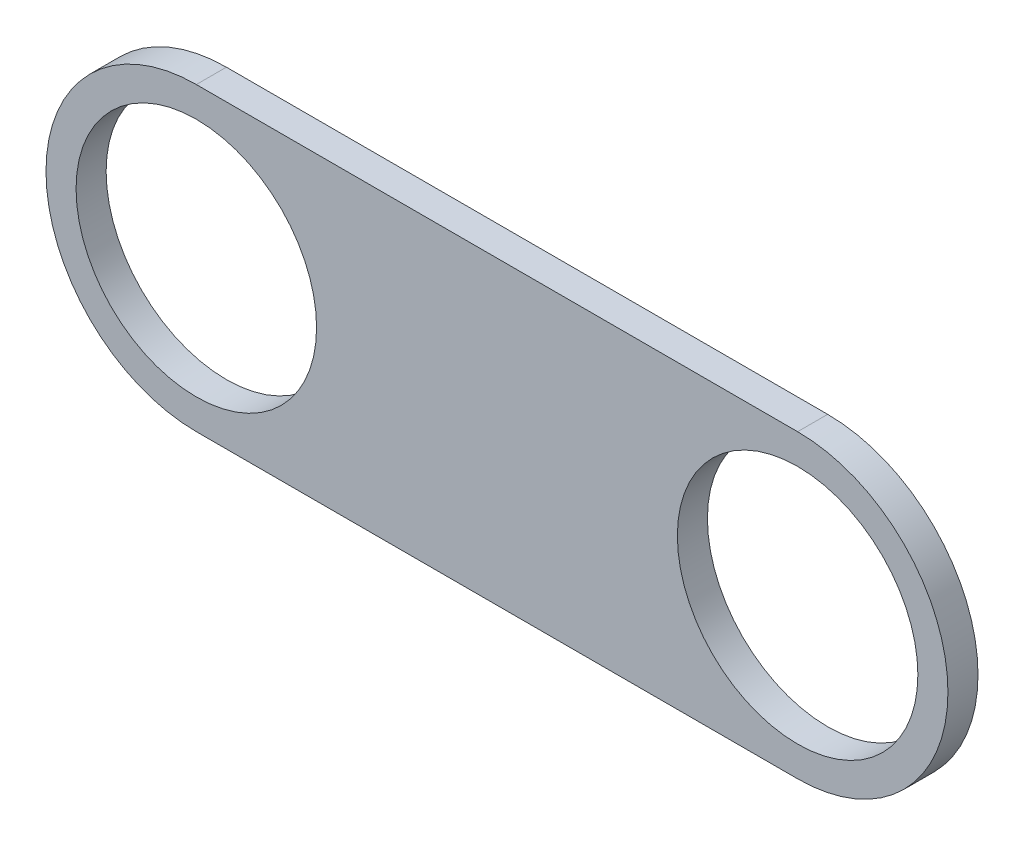
SolidWorks part; units mm, degrees
ref_plane "Front Plane" through (0, 0, 0) normal (0, 0, 1) x (1, 0, 0)
ref_plane "Top Plane" through (0, 0, 0) normal (0, 1, 0) x (1, 0, 0)
ref_plane "Right Plane" through (0, 0, 0) normal (1, 0, 0) x (0, 0, -1)
sketch "Sketch1" plane through (0, 0, 0) normal (0, 0, 1) x (1, 0, 0)
  line L0 (-83.6112, -57.9419) -> (-58.2112, -57.9419) construction
  line L1 (-83.6112, -51.5919) -> (-58.2112, -51.5919)
  line L2 (-83.6112, -64.2919) -> (-58.2112, -64.2919)
  arc A0 (-83.6112, -51.5919) -> (-83.6112, -64.2919) centre (-83.6112, -57.9419) ccw
  arc A1 (-58.2112, -64.2919) -> (-58.2112, -51.5919) centre (-58.2112, -57.9419) ccw
  circle A2 centre (-58.2112, -57.9419) radius 5.08
  circle A3 centre (-83.6112, -57.9419) radius 5.08
  point P2 (-70.9112, -57.9419)
  dimension "D1" = 12.7
  dimension "D2" = 25.4
extrude "Boss-Extrude1" add sketch "Sketch1" along normal blind 1.27
